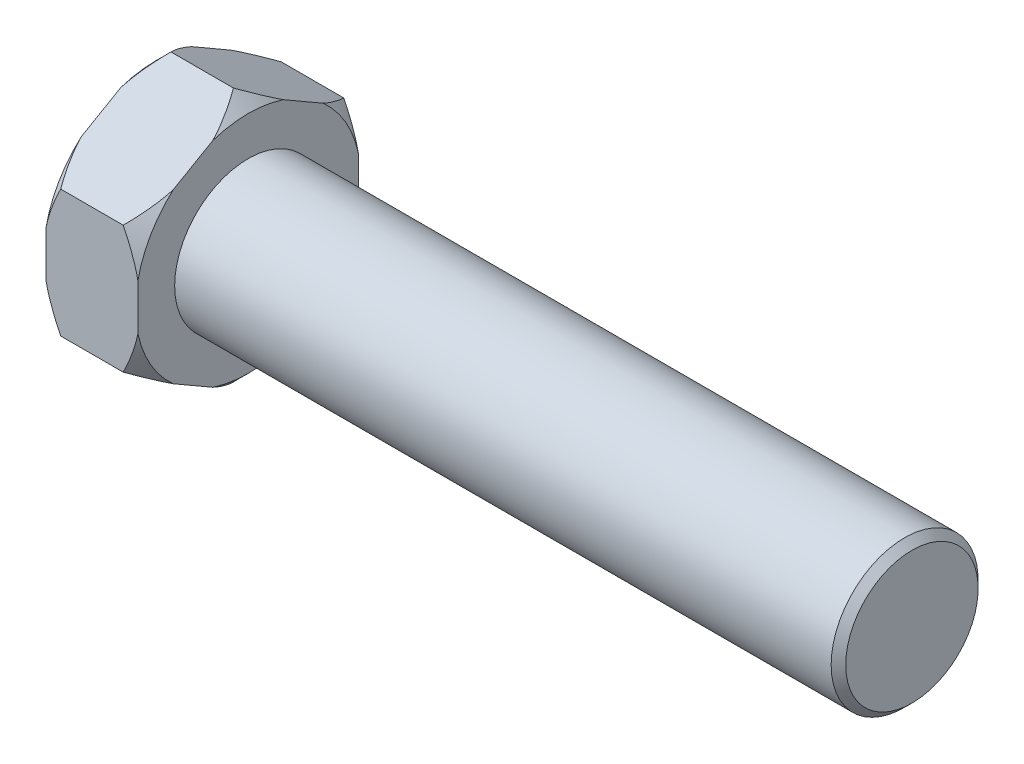
SolidWorks part; units mm, degrees
ref_plane "Plano frontal" through (0, 0, 0) normal (0, 0, 1) x (1, 0, 0)
ref_plane "Plano superior" through (0, 0, 0) normal (0, 1, 0) x (1, 0, 0)
ref_plane "Plano direito" through (0, 0, 0) normal (1, 0, 0) x (0, 0, -1)
ref_plane "Plano1" through (0, 0, 0) normal (0, 0, 1) x (1, 0, 0)
sketch "Esboço1" plane through (0, 0, 0) normal (0, 0, 1) x (1, 0, 0)
  line L0 (-11.9126, 0) -> (-11.9126, 14.5923)
  line L1 (-11.9126, 14.5923) -> (-9.4996, 17.0053)
  line L2 (-9.4996, 17.0053) -> (-2.413, 17.0053)
  line L3 (-2.413, 17.0053) -> (0, 14.5923)
  line L4 (0, 14.5923) -> (0, 9.525)
  line L5 (0, 9.525) -> (85.09, 9.525)
  line L6 (85.09, 9.525) -> (86.0362, 8.5789)
  line L7 (86.0362, 8.5789) -> (86.0362, 0)
  line L8 (86.0362, 0) -> (-11.9126, 0)
  line L9 (86.0362, 0) -> (-11.9126, 0) construction
revolve "Revolução1" add sketch "Esboço1" angle 360 about L9
cosmetic thread "Representação de rosca1" parameters "D1"=22.8203, "D2"=17.1577
ref_plane "Plano2" through (0, 0, 0) normal (1, 0, 0) x (0, 0, -1)
sketch "Esboço2" plane through (0, 0, 0) normal (1, 0, 0) x (0, 0, -1)
  line L0 (-14.2875, -8.2489) -> (0, -16.4978)
  line L1 (0, -16.4978) -> (14.2875, -8.2489)
  line L2 (14.2875, -8.2489) -> (14.2875, 8.2489)
  line L3 (14.2875, 8.2489) -> (0, 16.4978)
  line L4 (0, 16.4978) -> (-14.2875, 8.2489)
  line L5 (-14.2875, 8.2489) -> (-14.2875, -8.2489)
  circle A0 centre (0, 0) radius 28.575
extrude "Corte-extrusão1" cut sketch "Esboço2" against normal blind 11.9126
